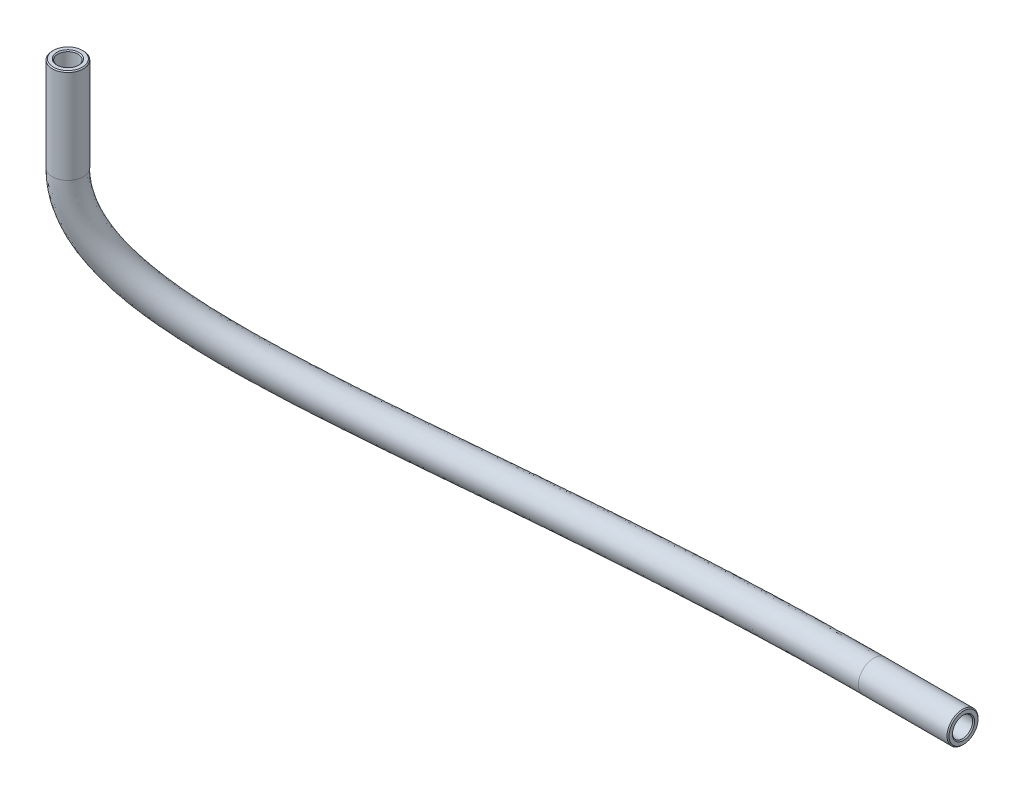
SolidWorks part; units mm, degrees
ref_plane "Front Plane" through (0, 0, 0) normal (0, 0, 1) x (1, 0, 0)
ref_plane "Top Plane" through (0, 0, 0) normal (0, 1, 0) x (1, 0, 0)
ref_plane "Right Plane" through (0, 0, 0) normal (1, 0, 0) x (0, 0, -1)
sketch3d "3DSketch1"
  line L0 (156.825, -62.125, 13.85) -> (156.825, -74.325, 13.85)
  line L1 (249.105, -102.4823, -9.525) -> (237.525, -102.4823, -9.525)
  spline S0 degree 3 poles (237.525, -102.4823, -9.525) (208.5929, -102.4823, -9.525) (170.4717, -97.3071, 2.1625) (156.825, -82.9175, 13.85) (156.825, -74.325, 13.85) knots 0 0 0 0 0.541354 1 1 1 1
sketch "Sketch1" plane through (239.725, 0, 0) normal (-1, 0, 0) x (0, 0, 1)
  circle A0 centre (-9.525, -102.4823) radius 2
  circle A1 centre (-9.525, -102.4823) radius 1.3
  circle A2 centre (-9.525, -102.4823) radius 3.5386 construction
  dimension "D1" = 2.6
  dimension "D2" = 4
sweep "Sweep1" add profiles "Sketch1" path "3DSketch1"
chamfer "Chamfer1" distance 0.127 angle 45 4 edges at (249.105, -104.4823, -9.525) (249.105, -103.7823, -9.525) (156.1711, -62.125, 15.7401) (156.4, -62.125, 15.0786)
